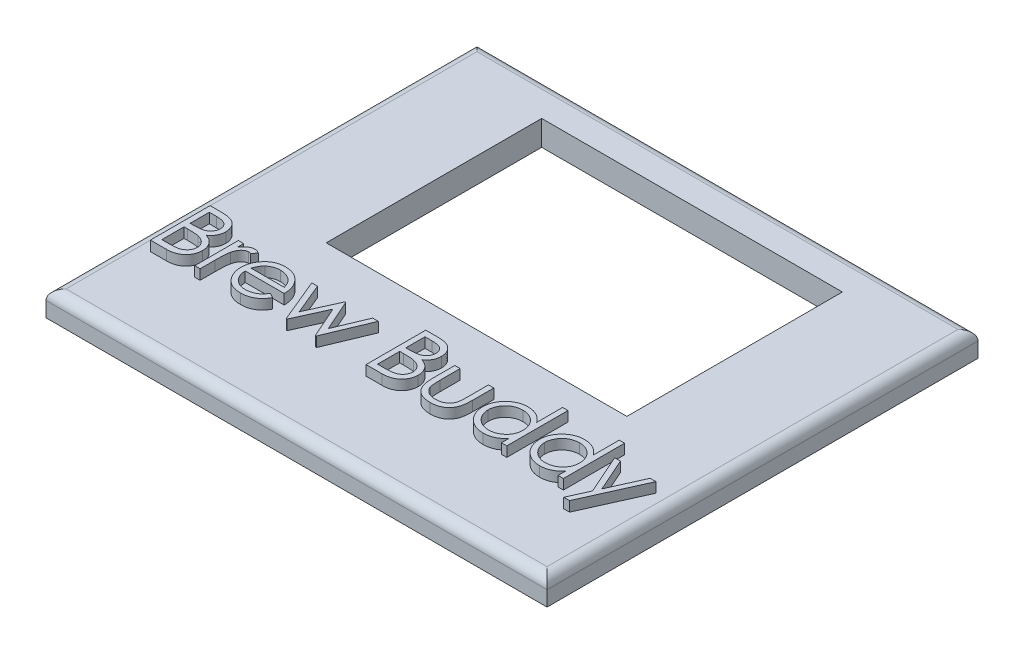
SolidWorks part; units mm, degrees
ref_plane "Front Plane" through (0, 0, 0) normal (0, 0, 1) x (1, 0, 0)
ref_plane "Top Plane" through (0, 0, 0) normal (0, 1, 0) x (1, 0, 0)
ref_plane "Right Plane" through (0, 0, 0) normal (1, 0, 0) x (0, 0, -1)
sketch "Sketch1" plane through (0, 0, 0) normal (0, 1, 0) x (1, 0, 0)
  line L1 (50, -43) -> (-50, -43)
  line L2 (50, -43) -> (50, 43)
  line L3 (50, 43) -> (-50, 43)
  line L4 (-50, -43) -> (-50, 43)
  line L5 (50, -43) -> (-50, 43) construction
  line L6 (50, 43) -> (-50, -43) construction
  point P0 (0, 0)
  dimension "D1" = 100
  dimension "D2" = 86
extrude "Boss-Extrude1" add sketch "Sketch1" along normal blind 5
sketch "Sketch2" plane through (0, 5, 0) normal (0, 1, 0) x (1, 0, 0)
  line L0 (-50, 43) -> (-50, -43) construction
  line L1 (30, -7.0735) -> (-30, -7.0735)
  line L2 (30, -7.0735) -> (30, 35.9265)
  line L3 (30, 35.9265) -> (-30, 35.9265)
  line L4 (-30, -7.0735) -> (-30, 35.9265)
  line L5 (30, -7.0735) -> (-30, 35.9265) construction
  line L6 (30, 35.9265) -> (-30, -7.0735) construction
  point P0 (0, 14.4265)
  dimension "D1" = 60
  dimension "D2" = 43
  dimension "D3" = 20
extrude "Cut-Extrude1" cut sketch "Sketch2" against normal blind 5
sketch "Sketch4" plane through (0, 5, 0) normal (0, 1, 0) x (1, 0, 0)
  line L0 (0, -7.0735) -> (0, -43) construction
  line L1 (-30, -7.0735) -> (30, -7.0735) construction
  line L2 (-50, -43) -> (50, -43) construction
  text T0 "Brew Buddy" font "Century Gothic" height in points 45
extrude "Boss-Extrude2" add sketch "Sketch4" along normal blind 2
fillet "Fillet1" radius 2 4 edges at (0, 5, 43) (50, 5, 0) (0, 5, -43) (-50, 5, 0)
sketch "Sketch5" plane through (0, 0, 0) normal (0, -1, 0) x (-1, 0, 0)
  line L0 (50, 43) -> (-50, -43) construction
  line L1 (50, -43) -> (-50, 43) construction
  line L2 (0, 43) -> (0, -43) construction
  line L3 (-50, 43) -> (50, 43) construction
  line L4 (50, -43) -> (-50, -43) construction
  line L5 (50, 0) -> (-50, 0) construction
  line L6 (50, 43) -> (50, -43) construction
  line L7 (-50, -43) -> (-50, 43) construction
  circle A0 centre (46.5882, 40.0658) radius 2.65
  circle A1 centre (46.5882, -40.0658) radius 2.65
  circle A2 centre (-46.5882, 40.0658) radius 2.65
  circle A3 centre (-46.5882, -40.0658) radius 2.65
  dimension "D1" = 5.3
  dimension "D2" = 4.5
extrude "Cut-Extrude2" cut sketch "Sketch5" against normal blind 3
